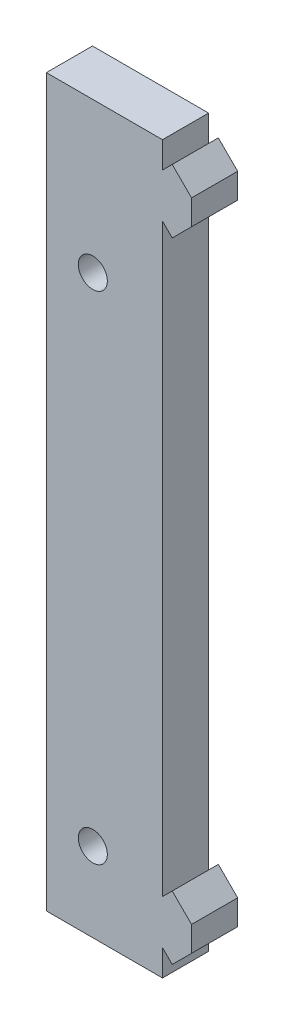
SolidWorks part; units mm, degrees
ref_plane "Front Plane" through (0, 0, 0) normal (0, 0, 1) x (1, 0, 0)
ref_plane "Top Plane" through (0, 0, 0) normal (0, 1, 0) x (1, 0, 0)
ref_plane "Right Plane" through (0, 0, 0) normal (1, 0, 0) x (0, 0, -1)
sketch "Sketch1" plane through (0, 0, 0) normal (0, 0, 1) x (1, 0, 0)
  line L0 (0, -2.7168) -> (1.0048, -1.712)
  line L1 (-40.8, 0) -> (0, 0) construction
  line L2 (-40.8, 0) -> (-40.8, -81.8) construction
  line L3 (-40.8, -81.8) -> (0, -81.8) construction
  line L4 (0, 0) -> (0, -2.7168) construction
  line L5 (-12, -75) -> (0, -75)
  line L6 (-12, -75) -> (-12, 0)
  line L7 (-12, 0) -> (0, 0)
  line L8 (0, -75) -> (0, -72.2832)
  line L9 (1.0048, -1.712) -> (3, -3.7071)
  line L10 (3, -3.7071) -> (3, -6.2929)
  line L11 (3, -6.2929) -> (1.0048, -8.288)
  line L12 (1.0048, -8.288) -> (0, -7.2832)
  line L13 (3, -5) -> (-5.5107, -5) construction
  line L14 (0, 0) -> (5, -5) construction
  line L15 (5, -5) -> (0, -10) construction
  line L16 (0, -7.2832) -> (0, -67.7168) construction
  line L17 (0, -2.7168) -> (0, 0)
  line L18 (0, -72.2832) -> (1.0048, -73.288)
  line L19 (1.0048, -73.288) -> (3, -71.2929)
  line L20 (3, -71.2929) -> (3, -68.7071)
  line L21 (3, -68.7071) -> (1.0048, -66.712)
  line L22 (1.0048, -66.712) -> (0, -67.7168)
  line L23 (0, -67.7168) -> (0, -7.2832)
  line L24 (0, -72.2832) -> (0, -81.8) construction
  line L25 (3, -70) -> (-1.5763, -70) construction
  circle A0 centre (-7.2, -15.5) radius 1.5
  circle A1 centre (-7.2, -66.8) radius 1.5
  dimension "D4" = 3
  dimension "D1" = 40.8
  dimension "D2" = 81.8
  dimension "D3" = 7.2
  dimension "D5" = 15.5
  dimension "D6" = 66.8
  dimension "D7" = 12
  dimension "D8" = 75
  dimension "D9" = 5
  dimension "D10" = 3
  dimension "D11" = 10
  dimension "D12" = 0.5
  dimension "D13" = 5.15
  dimension "D14" = 5
extrude "Boss-Extrude1" add sketch "Sketch1" along normal blind 4.7625
